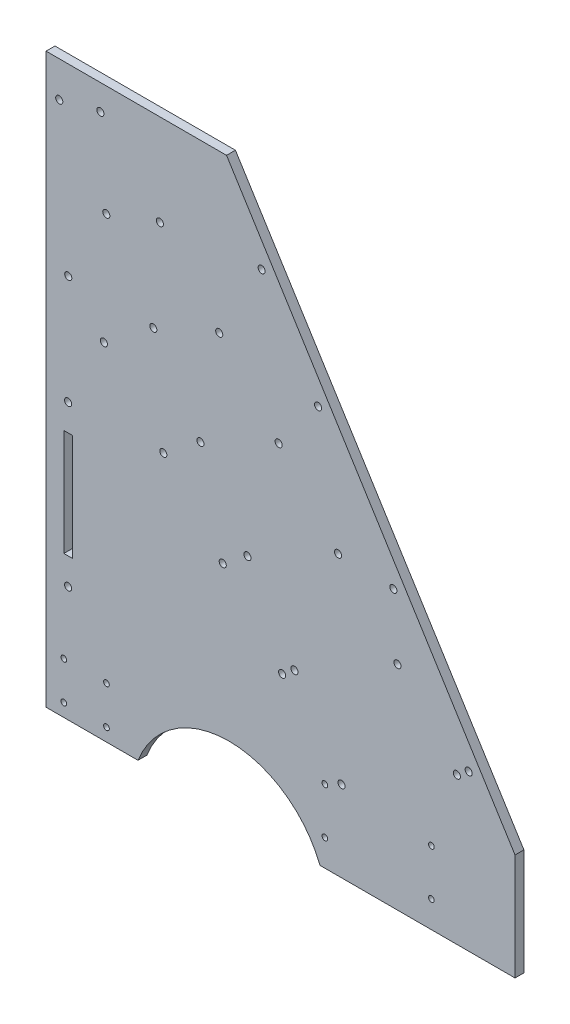
SolidWorks part; units mm, degrees
ref_plane "Front Plane" through (0, 0, 0) normal (0, 0, 1) x (1, 0, 0)
ref_plane "Top Plane" through (0, 0, 0) normal (0, 1, 0) x (1, 0, 0)
ref_plane "Right Plane" through (0, 0, 0) normal (1, 0, 0) x (0, 0, -1)
sketch "Sketch1" plane through (0, 0, 0) normal (0, 0, 1) x (1, 0, 0)
  line L0 (0, 0) -> (0, 320)
  line L2 (381.3611, 0) -> (0, 0)
  line L3 (0, 320) -> (381.3611, 320)
  line L4 (381.3611, 320) -> (381.3611, 0)
  dimension "D1" = 320
extrude "Boss-Extrude1" add sketch "Sketch1" along normal blind 5
sketch "Sketch2" plane through (0, 0, 5) normal (0, 0, 1) x (1, 0, 0)
  line L1 (0, 320) -> (0, 0) construction
  line L2 (381.3611, 320) -> (0, 320) construction
  circle A0 centre (103, -20) radius 55
  dimension "D1" = 110
  dimension "D3" = 340
  dimension "D2" = 103
extrude "Cut-Extrude1" cut sketch "Sketch2" against normal blind 5
sketch "Sketch3" plane through (0, 0, 5) normal (0, 0, 1) x (1, 0, 0)
  line L0 (333.3581, -64.9974) -> (106.6419, 297.8244)
  line L1 (154.2348, 0) -> (381.3611, 0) construction
  line L2 (0, 320) -> (0, 0) construction
  circle A0 centre (301.563, -14.1145) radius 2
  circle A1 centre (269.7678, 36.7684) radius 2
  circle A2 centre (237.9726, 87.6512) radius 2
  circle A3 centre (195.5791, 155.4951) radius 2
  circle A4 centre (153.1856, 223.3389) radius 2
  circle A5 centre (121.3904, 274.2218) radius 2
  point P16 (220, 116.4135)
  dimension "D1" = 60
  dimension "D2" = 60
  dimension "D3" = 60
  dimension "D4" = 80
  dimension "D5" = 80
  dimension "D6" = 60
  dimension "D7" = 58
  dimension "D8" = 220
extrude "Cut-Extrude2" cut sketch "Sketch3" against normal blind 5 contours L0 A5 | L0 A5 | L0 A4 | L0 A4 | L0 A3 | L0 A3 | L0 A2 | L0 A2 | L0 A1 | L0 A1 | L0 A0 | L0 A0
sketch "Sketch4" plane through (0, 0, 0) normal (0, 0, -1) x (-1, 0, 0)
  line L0 (-381.3611, 60) -> (-381.3611, 320)
  line L1 (-381.3611, 320) -> (-66.603, 320)
  circle A0 centre (-217, 41) radius 1.6
  circle A1 centre (-217, 15) radius 1.6
  circle A2 centre (-157, 41) radius 1.6
  circle A3 centre (-157, 15) radius 1.6
sketch "Sketch6" plane through (0, 0, 5) normal (0, 0, 1) x (1, 0, 0)
  circle A0 centre (10, 28.7) radius 1.6
  circle A1 centre (34, 28.7) radius 1.6
  circle A2 centre (10, 7.3) radius 1.6
  circle A3 centre (34, 7.3) radius 1.6
  circle A4 centre (310, 28.7) radius 1.6
  circle A5 centre (334, 28.7) radius 1.6
  circle A6 centre (334, 7.3) radius 1.6
  circle A7 centre (310, 7.3) radius 1.6
extrude "Cut-Extrude5" cut sketch "Sketch6" against normal blind 5
sketch "Sketch7" plane through (0, 0, 5) normal (0, 0, 1) x (1, 0, 0)
  line L0 (101.6289, 320) -> (264.0949, 60)
  line L1 (121.3904, 274.2218) -> (237.9726, 87.6512) construction
  line L2 (381.3611, 320) -> (0, 320) construction
  line L6 (381.3611, 60) -> (264.0949, 60)
  line L7 (381.3611, 0) -> (381.3611, 320) construction
  line L8 (154.2348, 0) -> (381.3611, 0) construction
  line L9 (101.6289, 320) -> (381.3611, 320)
  line L10 (381.3611, 320) -> (381.3611, 60)
  dimension "D1" = 7.5
  dimension "D3" = 60
extrude "Cut-Extrude6" cut sketch "Sketch7" against normal blind 10
extrude "Cut-Extrude7" cut sketch "Sketch4" against normal blind 10 contours A2 | A3 | A1 | A0
sketch "Sketch8" plane through (0, 0, 5) normal (0, 0, 1) x (1, 0, 0)
  line L1 (154.2348, 0) -> (381.3611, 0) construction
  line L2 (212.7662, 0) -> (381.3611, 0)
  line L3 (381.3611, 0) -> (381.3611, 89.7594)
  line L6 (264.0949, 60) -> (264.0949, 89.7594)
  line L7 (264.0949, 89.7594) -> (381.3611, 89.7594)
  line L9 (381.3611, 60) -> (264.0949, 60) construction
  line L10 (264.0949, 60) -> (264.0949, 0)
  dimension "D1" = 0
extrude "Cut-Extrude8" cut sketch "Sketch8" against normal blind 31.5
sketch "Sketch9" plane through (0, 0, 5) normal (0, 0, 1) x (1, 0, 0)
  line L1 (101.6289, 320) -> (0, 320) construction
  line L2 (1.3029, 323.9275) -> (213.2706, -15.2918) construction
  circle A0 centre (7.4106, 300) radius 2
  circle A1 centre (33.9066, 257.5976) radius 2
  circle A2 centre (60.4025, 215.1952) radius 2
  circle A3 centre (86.8985, 172.7928) radius 2
  circle A4 centre (113.3945, 130.3904) radius 2
  circle A5 centre (139.8904, 87.988) radius 2
  circle A6 centre (166.3864, 45.5856) radius 2
  dimension "D1" = 7.5
  dimension "D2" = 20
  dimension "D3" = 7
extrude "Cut-Extrude9" cut sketch "Sketch9" against normal blind 10
sketch "Sketch10" plane through (0, 0, 5) normal (0, 0, 1) x (1, 0, 0)
  line L0 (166.3864, 45.5856) -> (7.4106, 300)
  line L1 (166.3864, 45.5856) -> (37.1662, 189.0992)
  line L2 (37.1662, 189.0992) -> (0, 230.3764)
  line L3 (0, 320) -> (0, 0) construction
  circle A0 centre (99.4733, 119.9001) radius 2
  circle A1 centre (66.0168, 157.0573) radius 2
  circle A2 centre (132.9299, 82.7428) radius 2
  circle A3 centre (166.3864, 45.5856) radius 2 construction
  circle A4 centre (32.5603, 194.2145) radius 2
  circle A5 centre (12.4863, 216.5089) radius 2
  dimension "D2" = 50
  dimension "D3" = 50
  dimension "D4" = 50
  dimension "D5" = 50
  dimension "D6" = 30
  dimension "D1" = 10
extrude "Cut-Extrude10" cut sketch "Sketch10" against normal blind 10 contours L2 A5 | L2 A5 | L2 A4 | L2 A4 | L1 A1 | L1 A1 | L1 A0 | L1 A0 | L1 A2 | L1 A2
sketch "Sketch11" plane through (0, 0, 5) normal (0, 0, 1) x (1, 0, 0)
  line L0 (121.3904, 274.2218) -> (237.9726, 87.6512)
  line L1 (237.9726, 87.6512) -> (304.5854, -16.8247)
sketch "Sketch12" plane through (0, 0, 5) normal (0, 0, 1) x (1, 0, 0)
  line L0 (166.3864, 45.5856) -> (264.7933, 45.5856)
  line L2 (237.9726, 87.6512) -> (304.5854, -16.8247) construction
  line L3 (166.3864, 45.5856) -> (12.4863, 216.5089)
  line L4 (264.7933, 45.5856) -> (17.7094, 320)
  line L5 (101.6289, 320) -> (0, 320) construction
  circle A1 centre (231.3367, 82.7428) radius 2
  circle A2 centre (197.8802, 119.9001) radius 2
  circle A3 centre (164.4237, 157.0573) radius 2
  circle A4 centre (130.9672, 194.2145) radius 2
  circle A5 centre (97.5106, 231.3718) radius 2
  circle A6 centre (64.0541, 268.529) radius 2
  circle A7 centre (30.5976, 305.6863) radius 2
  dimension "D1" = 50
  dimension "D2" = 50
  dimension "D3" = 50
  dimension "D4" = 50
  dimension "D5" = 50
  dimension "D6" = 50
  dimension "D7" = 50
extrude "Cut-Extrude11" cut sketch "Sketch12" against normal blind 10 contours L4 A7 | L4 A7 | L4 A6 | L4 A6 | L4 A5 | L4 A5 | L4 A4 | L4 A4 | L4 A3 | L4 A3 | L4 A2 | L4 A2 | L4 A1 | L4 A1
sketch "Sketch14" plane through (0, 0, 5) normal (0, 0, 1) x (1, 0, 0)
  line L0 (0, 0) -> (51.7652, 0) construction
  line L1 (14.8, 80) -> (10, 80)
  line L2 (14.8, 80) -> (14.8, 140)
  line L3 (14.8, 140) -> (10, 140)
  line L4 (10, 80) -> (10, 140)
  line L5 (14.8, 80) -> (10, 140) construction
  line L6 (14.8, 140) -> (10, 80) construction
  line L7 (0, 320) -> (0, 0) construction
  point P0 (12.4, 110)
  dimension "D1" = 4.8
  dimension "D2" = 60
  dimension "D3" = 80
  dimension "D4" = 10
extrude "Cut-Extrude12" cut sketch "Sketch14" against normal blind 5
sketch "Sketch15" plane through (0, 0, 5) normal (0, 0, 1) x (1, 0, 0)
  line L0 (14.8, 80) -> (14.8, 140) construction
  circle A0 centre (12.4, 155) radius 2
  circle A1 centre (12.4, 65) radius 2
  point P4 (14.8, 110)
  dimension "D1" = 45
  dimension "D2" = 45
extrude "Cut-Extrude13" cut sketch "Sketch15" against normal blind 5
